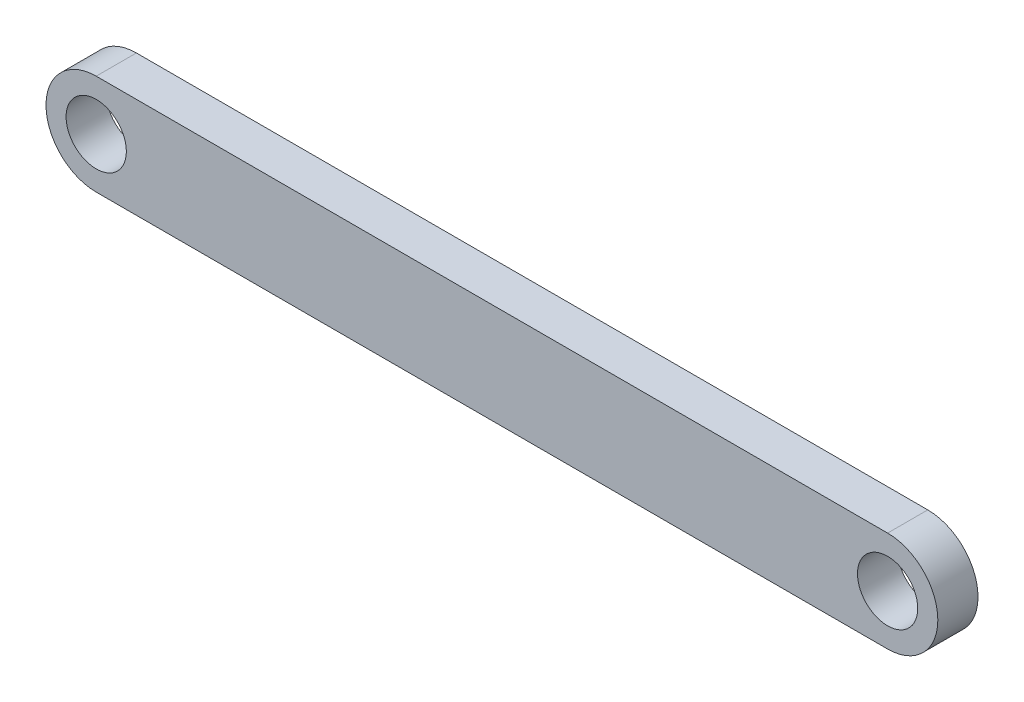
SolidWorks part; units mm, degrees
ref_plane "Front Plane" through (0, 0, 0) normal (0, 0, 1) x (1, 0, 0)
ref_plane "Top Plane" through (0, 0, 0) normal (0, 1, 0) x (1, 0, 0)
ref_plane "Right Plane" through (0, 0, 0) normal (1, 0, 0) x (0, 0, -1)
sketch "Sketch1" plane through (0, 0, 0) normal (0, 0, 1) x (1, 0, 0)
  line L0 (-0.0634, -1.3364) -> (39.3366, -1.3364) construction
  line L1 (-0.0634, 1.1636) -> (39.3366, 1.1636)
  line L2 (-0.0634, -3.8364) -> (39.3366, -3.8364)
  arc A0 (-0.0634, 1.1636) -> (-0.0634, -3.8364) centre (-0.0634, -1.3364) ccw
  arc A1 (39.3366, -3.8364) -> (39.3366, 1.1636) centre (39.3366, -1.3364) ccw
  circle A2 centre (-0.0634, -1.3364) radius 1.5
  circle A3 centre (39.3366, -1.3364) radius 1.5
  point P2 (19.6366, -1.3364)
  dimension "D3" = 3
  dimension "D4" = 3
  dimension "D1" = 39.4
  dimension "D2" = 5
extrude "Boss-Extrude1" add sketch "Sketch1" along normal blind 2
